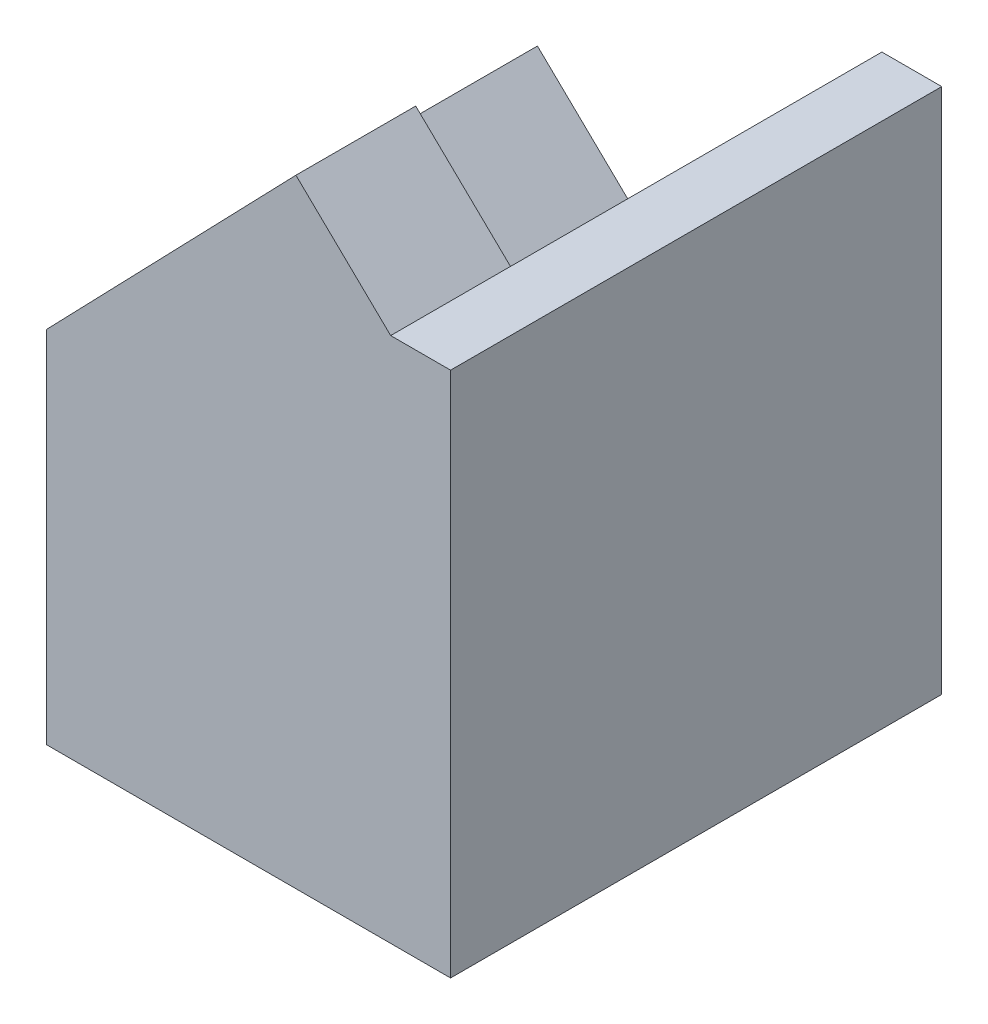
SolidWorks part; units mm, degrees
ref_plane "Front Plane" through (0, 0, 0) normal (0, 0, 1) x (1, 0, 0)
ref_plane "Top Plane" through (0, 0, 0) normal (0, 1, 0) x (1, 0, 0)
ref_plane "Right Plane" through (0, 0, 0) normal (1, 0, 0) x (0, 0, -1)
sketch "Sketch1" plane through (0, 0, 0) normal (0, 0, 1) x (1, 0, 0)
  line L0 (0, 0) -> (6.75, 0)
  line L1 (6.75, 0) -> (6.75, 4.7883)
  line L2 (6.75, 4.7883) -> (5.75, 4.7883)
  line L3 (5.75, 4.7883) -> (4.168, 6.316)
  line L4 (4.168, 6.316) -> (0, 2)
  line L5 (0, 2) -> (0, 0)
  dimension "D1" = 6.75
  dimension "D2" = 2
  dimension "D3" = 1
  dimension "D4" = 136
  dimension "D5" = 6
extrude "Boss-Extrude1" add sketch "Sketch1" along normal blind 8.2
sketch "Sketch2" plane through (-0.9994, 0.9651, 0) normal (-0.7193, 0.6947, 0) x (0.6947, 0.7193, 0)
  line L0 (8.4387, 0) -> (8.4387, -6.2)
  line L2 (8.4387, -6.2) -> (3.4387, -6.2)
  line L3 (3.4387, -6.2) -> (3.4387, -6.45)
  line L4 (1.4387, -8.2) -> (1.4387, 0) construction
  line L5 (1.4387, -6.45) -> (1.4387, 0)
  line L6 (1.4387, 0) -> (8.4387, 0)
  arc A0 (3.4387, -6.45) -> (1.4387, -6.45) centre (2.4387, -6.45) cw
  dimension "D1" = 6.2
  dimension "D2" = 2
  dimension "D3" = 0.25
  dimension "D4" = 7
extrude "Cut-Extrude1" cut sketch "Sketch2" against normal blind 2.2
sketch "Sketch3" plane through (0, 0, 0) normal (0, -1, 0) x (1, 0, 0)
  line L1 (0, 8.2) -> (6.75, 8.2)
  line L2 (0, 8.2) -> (0, 0)
  line L3 (0, 0) -> (6.75, 0)
  line L4 (6.75, 8.2) -> (6.75, 0)
extrude "Boss-Extrude2" add sketch "Sketch3" along normal blind 4
hole_wizard "M2x0.4 Tapped Hole1" positions "Sketch5" profile "Sketch4" tap size "M2x0.4" standard "ANSI Metric"
sketch "Sketch5" plane through (0, -4, 0) normal (0, -1, 0) x (-1, 0, 0)
  line L0 (-6.75, 0) -> (-6.75, -8.2) construction
  line L1 (-6.75, -8.2) -> (0, -8.2) construction
  point P0 (-3.75, -4.1)
  dimension "D1" = 3
  dimension "D2" = 4.1
sketch "Sketch4" plane through (3.75, -4, 4.1) normal (1, 0, 0) x (0, 0, -1)
  line L0 (0, 0) -> (0, 5.1807)
  line L1 (0, 5.1807) -> (0.8, 4.7)
  line L2 (0.8, 4.7) -> (0.8, 0)
  line L5 (0.8, 0) -> (0, 0)
  line L10 (0, 5.1807) -> (-0.8, 4.7) construction
  line L11 (0, -6.35) -> (0, 107.95) construction
  dimension "Tap Drill Dia." = 1.6
  dimension "Tap Drill Depth" = 4.7
  dimension "Drill Angle" = 118
cosmetic thread "Hole Thread1" parameters "D1"=3.5, "D2"=2
hole_wizard "Ø1.5mm Dowel Hole1" positions "Sketch7" profile "Sketch6" hole size "Ø1.5" standard "ISO"
sketch "Sketch7" plane through (0, -4, 0) normal (0, -1, 0) x (-1, 0, 0)
  line L0 (-6.75, -8.2) -> (-6.75, 0) construction
  line L1 (-6.75, 0) -> (-6.75, -8.2) construction
  point P0 (-3.75, -7.1)
  point P2 (-3.75, -1.1)
  point P5 (-6.75, -4.1)
  dimension "D1" = 6
  dimension "D2" = 3
  dimension "D3" = 3
sketch "Sketch6" plane through (3.75, -4, 7.1) normal (1, 0, 0) x (0, 0, -1)
  line L0 (0, 0) -> (0, 3.4506)
  line L1 (0, 3.4506) -> (0.75, 3)
  line L2 (0.75, 3) -> (0.75, 0)
  line L5 (0.75, 0) -> (0, 0)
  line L10 (0, 3.4506) -> (-0.75, 3) construction
  line L11 (0, -6.35) -> (0, 107.95) construction
  dimension "Hole Dia." = 1.5
  dimension "Hole Depth" = 3
  dimension "Drill Angle" = 118
